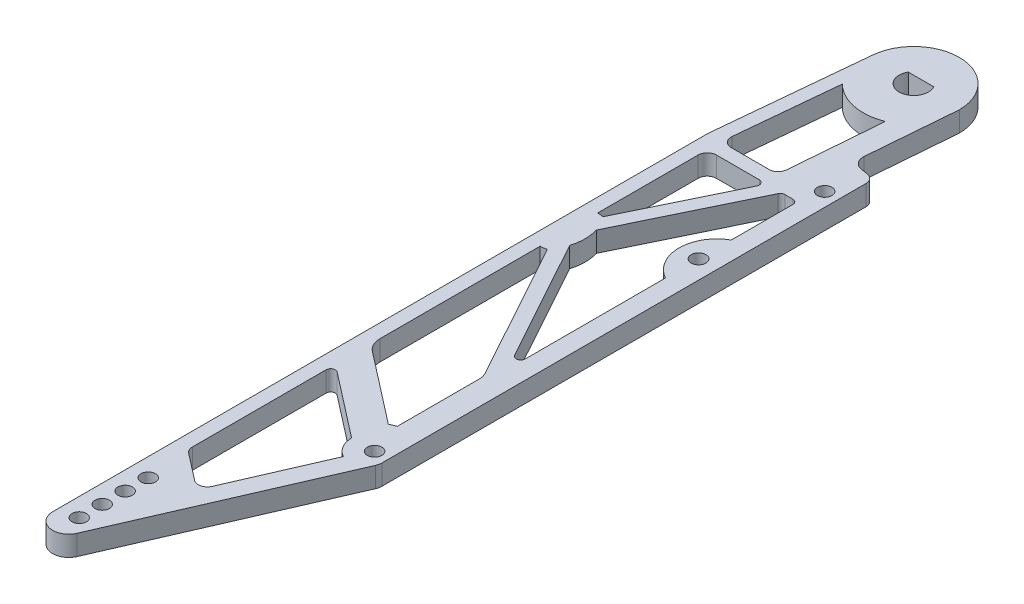
SolidWorks part; units mm, degrees
material "6061-T6 (SS)"
ref_plane "X-Y Datum" through (0, 0, 0) normal (0, 0, 1) x (1, 0, 0)
ref_plane "X-Z Datum" through (0, 0, 0) normal (0, 1, 0) x (1, 0, 0)
ref_plane "Y-Z Datum" through (0, 0, 0) normal (1, 0, 0) x (0, 0, -1)
other "Graphic1" [suppressed]
other "Graphic (Closed) -1" [suppressed]
sketch "Sketch2" plane through (0, 0, 0) normal (0, 1, 0) x (1, 0, 0)
  line L5 (13.4859, -162.4108) -> (-11.43, -143.082) construction
  line L8 (0, 0) -> (0, -24.13) construction
  line L11 (15.1556, -28.0184) -> (13.2387, -27.713)
  line L15 (-16.51, -221.3289) -> (-16.51, -40.4661)
  line L22 (-7.9887, -223.1013) -> (16.9799, -165.6775)
  line L23 (17.2959, -164.1583) -> (17.2959, -30.5268)
  line L33 (10.4385, -167.9818) -> (-0.5342, -193.2173)
  line L44 (-8.8047, -78.8772) -> (7.5755, -45.0536)
  line L45 (8.7185, -44.3372) -> (10.9459, -44.3372)
  line L47 (9.8331, -120.1049) -> (-8.8047, -86.2228)
  line L49 (-12.4315, -37.7433) -> (-9.7554, -9.9996)
  line L51 (5.1277, -12.9949) -> (3.0693, -38.194)
  line L53 (0.5377, -40.5272) -> (-9.9032, -40.5272)
  line L56 (1.663, -44.3372) -> (-10.16, -44.3372)
  line L57 (13.7382, -24.5776) -> (0, 0) construction
  line L58 (10.5738, -24.3191) -> (12.5603, 0)
  line L59 (-12.7, -149.6154) -> (-12.7, -186.5441)
  line L63 (7.1359, -162.4108) -> (-10.6516, -148.612)
  line L64 (-12.7, -74.6125) -> (-12.7, -46.8772)
  line L65 (2.8061, -46.1607) -> (-11.056, -74.7846)
  line L66 (-16.4983, -40.2222) -> (-12.5023, 1.2059)
  line L67 (-4.4204, -194.2114) -> (-11.7169, -188.551)
  line L68 (5.8058, -44.3372) -> (-12.7, -82.55) construction
  line L69 (-1.7326, -64.2739) -> (-5.1616, -62.6133) construction
  line L70 (8.9236, -154.0495) -> (-10.7338, -138.8001)
  line L71 (10.6561, -153.3158) -> (10.6561, -130.811)
  line L72 (10.0271, -128.3626) -> (-10.9185, -90.285)
  line L75 (-12.7, -134.7862) -> (-12.7, -90.4875)
  line L76 (-3.5217, 2) -> (3.5217, 2)
  line L78 (12.2159, -45.6072) -> (12.2159, -62.6181)
  line L79 (12.2159, -80.8) -> (12.2159, -119.4928)
  circle A0 centre (0, 0) radius 4.05
  circle A2 centre (-11.43, -219.075) radius 2
  circle A3 centre (-11.43, -212.725) radius 2
  circle A4 centre (-11.43, -206.375) radius 2
  circle A5 centre (-11.43, -200.025) radius 2
  circle A7 centre (0, 0) radius 12.5603 construction
  circle A12 centre (13.4859, -38.1) radius 2
  arc A13 (-12.5023, 1.2059) -> (12.5603, 0) centre (0, 0) cw
  arc A14 (-8.8047, -86.2228) -> (-8.8047, -78.8772) centre (-20.962, -82.55) ccw
  circle A16 centre (24.0125, -14.7036) radius 3.175 construction
  arc A17 (24.0125, -14.7036) -> (13.7382, -24.5776) centre (0, 0) cw construction
  circle A18 centre (13.7382, -24.5776) radius 3.175 construction
  arc A19 (13.2387, -27.713) -> (10.5738, -24.3191) centre (13.7382, -24.5776) cw
  arc A20 (15.1556, -28.0184) -> (17.2959, -30.5268) centre (14.7559, -30.5268) cw
  circle A21 centre (13.4859, -162.4108) radius 2
  arc A24 (10.4385, -167.9818) -> (7.1359, -162.4108) centre (13.4859, -162.4108) cw
  arc A25 (-16.51, -221.3289) -> (-7.9887, -223.1013) centre (-12.065, -221.3289) ccw
  arc A26 (-12.7, -74.6125) -> (-11.056, -74.7846) centre (-12.7, -82.55) cw
  arc A28 (5.1277, -12.9949) -> (-9.7554, -9.9996) centre (0, 0) cw
  arc A31 (-10.16, -44.3372) -> (-12.7, -46.8772) centre (-10.16, -46.8772) ccw
  arc A32 (-12.4315, -37.7433) -> (-9.9032, -40.5272) centre (-9.9032, -37.9872) ccw
  arc A33 (0.5377, -40.5272) -> (3.0693, -38.194) centre (0.5377, -37.9872) ccw
  arc A36 (-12.7, -149.6154) -> (-10.6516, -148.612) centre (-11.43, -149.6154) cw
  arc A37 (9.8331, -120.1049) -> (12.2159, -119.4928) centre (10.9459, -119.4928) ccw
  arc A38 (7.5755, -45.0536) -> (8.7185, -44.3372) centre (8.7185, -45.6072) cw
  arc A39 (10.9459, -44.3372) -> (12.2159, -45.6072) centre (10.9459, -45.6072) cw
  arc A40 (1.663, -44.3372) -> (2.8061, -46.1607) centre (1.663, -45.6072) cw
  arc A50 (17.2959, -164.1583) -> (16.9799, -165.6775) centre (13.4859, -164.1583) cw
  arc A52 (-16.4983, -40.2222) -> (-16.51, -40.4661) centre (-13.97, -40.4661) ccw
  arc A53 (-12.7, -186.5441) -> (-11.7169, -188.551) centre (-10.16, -186.5441) ccw
  arc A54 (-4.4204, -194.2114) -> (-0.5342, -193.2173) centre (-2.8635, -192.2045) ccw
  arc A55 (10.6561, -153.3158) -> (8.9236, -154.0495) centre (13.4859, -162.4108) ccw
  arc A56 (-10.9185, -90.285) -> (-12.7, -90.4875) centre (-12.7, -82.55) cw
  arc A57 (-12.7, -134.7862) -> (-10.7338, -138.8001) centre (-7.62, -134.7862) ccw
  arc A58 (10.0271, -128.3626) -> (10.6561, -130.811) centre (5.5761, -130.811) cw
  arc A59 (12.2159, -62.6181) -> (12.2159, -80.8) centre (17.2959, -71.7091) ccw
  circle A60 centre (12.2159, -71.7091) radius 2.032
  point P30 (17.2959, -28.3595)
  point P44 (-3.4471, -63.4436)
  point P45 (-1.8376, -196.215)
  point P75 (-4.05, 0)
  point P85 (12.2159, -71.7091)
  point P88 (-12.7, -44.3372)
  point P91 (-12.7, -40.5272)
  point P104 (10.6561, -121.6534)
  point P107 (7.9224, -44.3372)
  point P110 (12.2159, -44.3372)
  point P120 (17.2959, -164.9508)
  dimension "D1" = 8.1
  dimension "D6" = 4
  dimension "D12" = 24.13
  dimension "D5" = 25.1206
  dimension "D14" = 5.08
  dimension "D19" = 4
  dimension "D20" = 6.35
  dimension "D24" = 3.81
  dimension "D50" = 12.7
  dimension "D51" = 8.262
  dimension "D42" = 3.81
  dimension "D62" = 6.35
  dimension "D63" = 29.204
  dimension "D27" = 2.54
  dimension "D44" = 4
  dimension "D18" = 4.445
  dimension "D34" = 3.81
  dimension "D36" = 6.35
  dimension "D33" = 13.97
  dimension "D38" = 3.81
  dimension "D39" = 8.89
  dimension "D48" = 2.54
  dimension "D49" = 1.27
  dimension "D52" = 3.81
  dimension "D53" = 3.81
  dimension "D54" = 9.525
  dimension "D58" = 2.54
  dimension "D59" = 3.81
  dimension "D64" = 2
  dimension "D65" = 10.414
  dimension "D29" = 7.9375
  dimension "D31" = 3.81
  dimension "D41" = 2.54
  dimension "D55" = 7.9375
  dimension "D57" = 5.08
  dimension "D66" = 10.8409
  dimension "D25" = 4.064
  dimension "D7" = 6.35
  dimension "D8" = 6.35
  dimension "D9" = 6.35
  dimension "D10" = 5.08
  dimension "D11" = 5.08
  dimension "D13" = 4.1084
  dimension "D15" = 82.55
  dimension "D16" = 12.7
  dimension "D17" = 13.7382
  dimension "D21" = 136.5913
  dimension "D22" = 38.1
  dimension "D23" = 13.4859
  dimension "D26" = 3.81
  dimension "D28" = 40.5272
  dimension "D30" = 2.54
  dimension "D32" = 3.81
  dimension "D35" = 3.81
  dimension "D37" = 16.51
  dimension "D40" = 23.5
  dimension "D43" = 200.025
  dimension "D45" = 6.35
  dimension "D46" = 6.35
  dimension "D47" = 4.2935
  dimension "D56" = 3.81
  dimension "D60" = 24.0125
  dimension "D61" = 14.7036
  dimension "D67" = 5.08
extrude "Boss-Extrude1" add sketch "Sketch2" along normal blind 5.588 contours L76 A0
sketch "Sketch6" plane through (-16.51, 0, 0) normal (-1, 0, 0) x (0, 0, 1)
  line L0 (183.2289, 5.588) -> (183.2289, 0)
  line L1 (221.3289, 0) -> (40.4661, 0) construction
  line L2 (221.3289, 5.588) -> (40.4661, 5.588) construction
  line L3 (221.3289, 5.588) -> (221.3289, 0) construction
  dimension "D1" = 38.1
split line "Split Line2"
sketch "Sketch7" plane through (0, 5.588, 0) normal (0, 1, 0) x (1, 0, 0)
  line L0 (17.2959, -164.1583) -> (17.2959, -30.5268) construction
  circle A0 centre (12.2159, -71.656) radius 2.032
  dimension "D3" = 4.064
  dimension "D1" = 5.08
  dimension "D2" = 9.144
extrude "Cut-Extrude1" cut sketch "Sketch7" against normal up to surface (5.588 mm away) up to face at (-0.889, 0, 127.6367)
